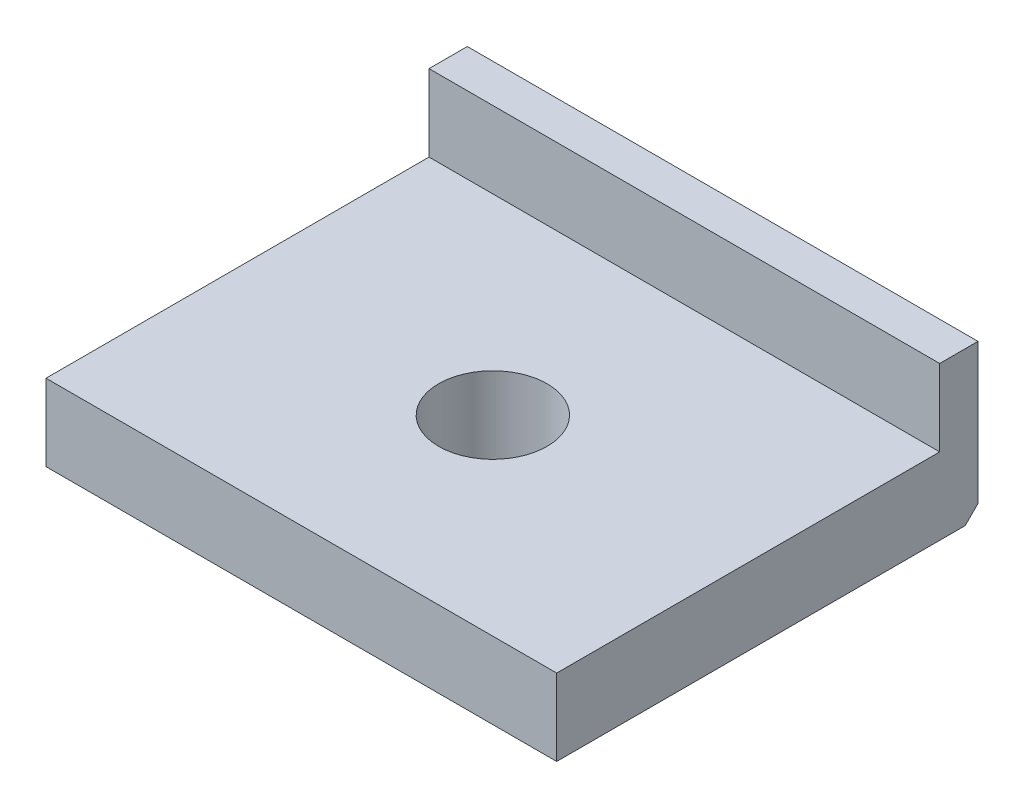
SolidWorks part; units mm, degrees
ref_plane "Front Plane" through (0, 0, 0) normal (0, 0, 1) x (1, 0, 0)
ref_plane "Top Plane" through (0, 0, 0) normal (0, 1, 0) x (1, 0, 0)
ref_plane "Right Plane" through (0, 0, 0) normal (1, 0, 0) x (0, 0, -1)
sketch "Sketch1" plane through (0, 0, 0) normal (0, 1, 0) x (1, 0, 0)
  line L1 (10, -9) -> (-10, -9)
  line L2 (10, -9) -> (10, 9)
  line L3 (10, 9) -> (-10, 9)
  line L4 (-10, -9) -> (-10, 9)
  line L5 (10, -9) -> (-10, 9) construction
  line L6 (10, 9) -> (-10, -9) construction
  point P0 (0, 0)
  dimension "D1" = 20
  dimension "D2" = 18
extrude "Boss-Extrude1" add sketch "Sketch1" along normal blind 6
sketch "Sketch2" plane through (0, 6, 0) normal (0, 1, 0) x (1, 0, 0)
  line L0 (10, -9) -> (10, 9) construction
  line L1 (-10, 9) -> (10, 9)
  line L2 (-10, 9) -> (-10, 6)
  line L3 (-10, 6) -> (10, 6)
  line L4 (10, 9) -> (10, 6)
  dimension "D1" = 3
extrude "Boss-Extrude2" add sketch "Sketch2" along normal blind 3
sketch "Sketch3" plane through (0, 0, 0) normal (0, -1, 0) x (1, 0, 0)
  line L0 (0, -1000) -> (0, 49000) construction
  line L1 (-1000, 1.5) -> (49000, 1.5) construction
  line L2 (-10, 9) -> (10, 9) construction
  circle A0 centre (0, 1.5) radius 2.125
  dimension "D3" = 4.25
  dimension "D1" = 7.5
  dimension "D2" = 0
extrude "Cut-Extrude1" cut sketch "Sketch3" against normal through all both and the other way through all
chamfer "Chamfer1" distance 3 angle 45 3 edges at (-10, 0, 0) (0, 0, 9) (10, 0, 0)
chamfer "Chamfer2" distance 5 angle 45 1 edges at (0, 0, -9)
chamfer "Chamfer3" distance 1.5 angle 45 3 edges at (-10, 7, -9) (0, 9, -9) (10, 7, -9)
